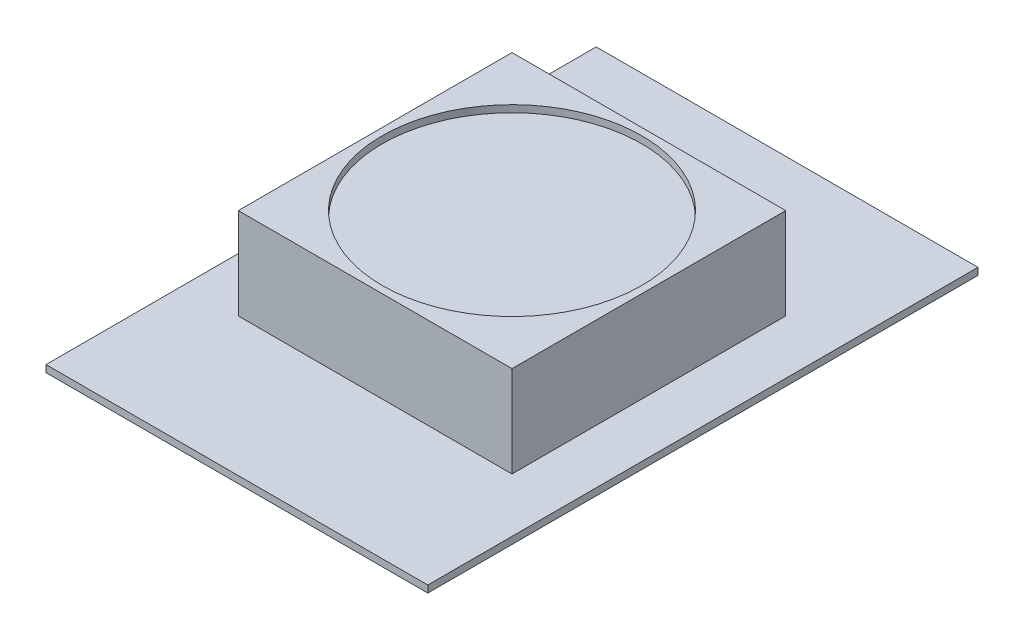
SolidWorks part; units mm, degrees
ref_plane "Front Plane" through (0, 0, 0) normal (0, 0, 1) x (1, 0, 0)
ref_plane "Top Plane" through (0, 0, 0) normal (0, 1, 0) x (1, 0, 0)
ref_plane "Right Plane" through (0, 0, 0) normal (1, 0, 0) x (0, 0, -1)
sketch "Sketch1" plane through (0, 0, 0) normal (0, 1, 0) x (1, 0, 0)
  line L0 (-3.4544, 4.9784) -> (3.4544, -4.9784) construction
  line L1 (-3.4544, 4.9784) -> (3.4544, 4.9784)
  line L2 (-3.4544, 4.9784) -> (-3.4544, -4.9784)
  line L3 (-3.4544, -4.9784) -> (3.4544, -4.9784)
  line L4 (3.4544, 4.9784) -> (3.4544, -4.9784)
  dimension "D1" = 9.9568
  dimension "D2" = 6.9088
extrude "Boss-Extrude1" add sketch "Sketch1" along normal blind 0.127
sketch "Sketch3" plane through (0, 0.127, 0) normal (0, 1, 0) x (1, 0, 0)
  line L0 (-3.4544, 4.9784) -> (3.4544, -4.9784) construction
  line L1 (-2.4765, 2.4765) -> (2.4765, -2.4765) construction
  line L2 (-2.4765, 2.4765) -> (2.4765, 2.4765)
  line L3 (-2.4765, 2.4765) -> (-2.4765, -2.4765)
  line L4 (-2.4765, -2.4765) -> (2.4765, -2.4765)
  line L5 (2.4765, 2.4765) -> (2.4765, -2.4765)
  dimension "D1" = 4.953
extrude "Boss-Extrude3" add sketch "Sketch3" along normal blind 1.651
sketch "Sketch5" plane through (0, 1.778, 0) normal (0, 1, 0) x (1, 0, 0)
  circle A0 centre (0, 0) radius 2.3483
extrude "Cut-Extrude1" cut sketch "Sketch5" against normal blind 0.127
pattern_linear "LPattern1" [suppressed] count 4 spacing 16.6116
